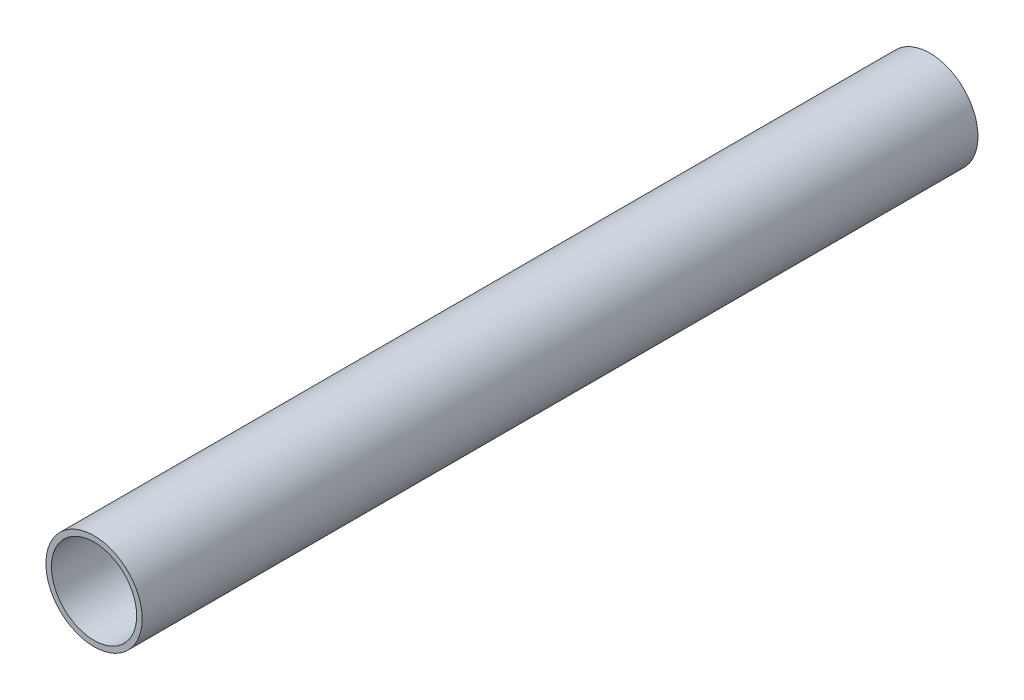
SolidWorks part; units mm, degrees
material "Paper"
ref_plane "Alzado" through (0, 0, 0) normal (0, 0, 1) x (1, 0, 0)
ref_plane "Planta" through (0, 0, 0) normal (0, 1, 0) x (1, 0, 0)
ref_plane "Vista lateral" through (0, 0, 0) normal (1, 0, 0) x (0, 0, -1)
sketch "Croquis1" plane through (0, 0, 0) normal (0, 0, 1) x (1, 0, 0)
  circle A0 centre (0, 0) radius 23.2
  circle A1 centre (0, 0) radius 26.2
  dimension "D1" = 52.4
  dimension "D2" = 46.4
extrude "Saliente-Extruir1" add sketch "Croquis1" along normal blind 455
equation "\"ODAblative\" = 52.4mm"
equation "\"D1@Croquis1\"=\"ODAblative\""
equation "\"IDAblative\"= \"ODAblative\" - \"AblativeThickness\" * 2"
equation "\"D2@Croquis1\"=\"IDAblative\""
equation "\"LengthAblative\"= 455mm"
equation "\"D1@Saliente-Extruir1\"=\"LengthAblative\""
equation "\"AblativeThickness\"= 3"
